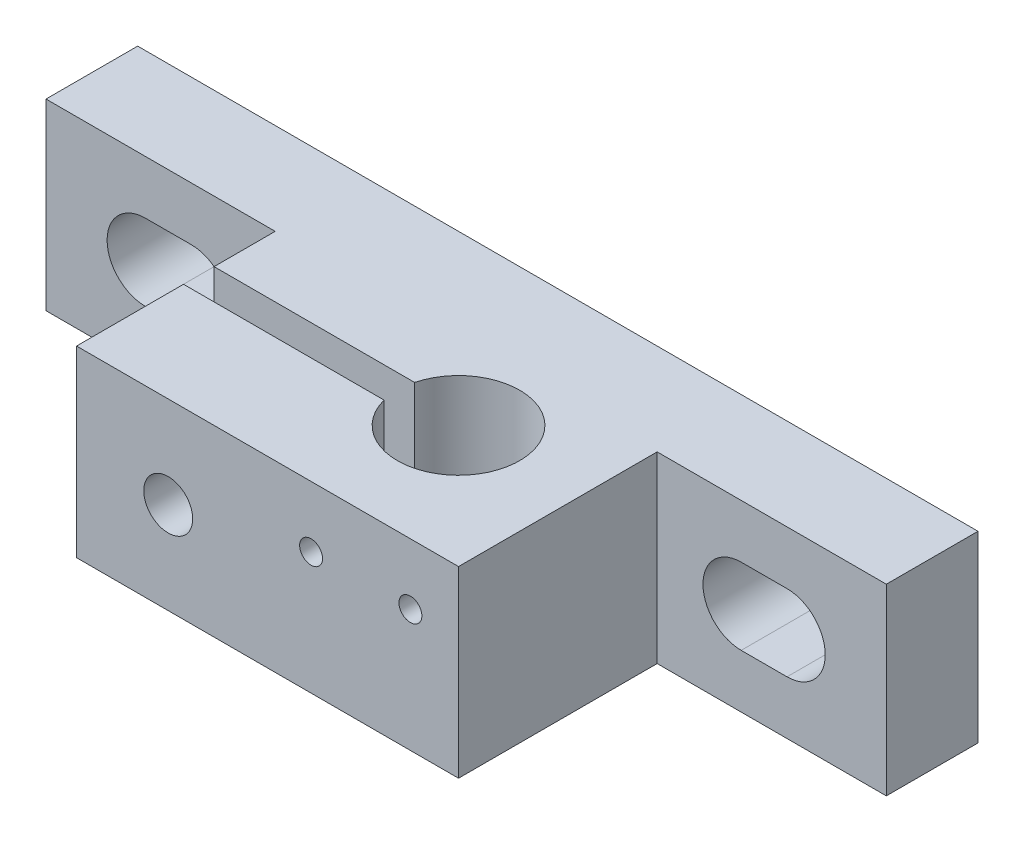
SolidWorks part; units mm, degrees
material "Copper"
ref_plane "Front Plane" through (0, 0, 0) normal (0, 0, 1) x (1, 0, 0)
ref_plane "Top Plane" through (0, 0, 0) normal (0, 1, 0) x (1, 0, 0)
ref_plane "Right Plane" through (0, 0, 0) normal (1, 0, 0) x (0, 0, -1)
sketch "Sketch2" plane through (0, 0, 0) normal (0, 0, 1) x (1, 0, 0)
  line L0 (6.5, 6) -> (9.5, 6) construction
  line L1 (0, 0) -> (55, 0)
  line L2 (0, 0) -> (0, 12)
  line L3 (0, 12) -> (55, 12)
  line L4 (55, 0) -> (55, 12)
  line L5 (27.5, 12) -> (27.5, -3.75) construction
  line L6 (6.5, 8.5) -> (9.5, 8.5)
  line L7 (6.5, 3.5) -> (9.5, 3.5)
  line L8 (48.5, 6) -> (45.5, 6) construction
  line L9 (48.5, 8.5) -> (45.5, 8.5)
  line L10 (48.5, 3.5) -> (45.5, 3.5)
  arc A0 (6.5, 8.5) -> (6.5, 3.5) centre (6.5, 6) ccw
  arc A1 (48.5, 8.5) -> (48.5, 3.5) centre (48.5, 6) cw
  arc A2 (9.5, 3.5) -> (9.5, 8.5) centre (9.5, 6) ccw
  arc A3 (45.5, 3.5) -> (45.5, 8.5) centre (45.5, 6) cw
  point P11 (8, 6)
  point P16 (47, 6)
  dimension "D1" = 6.5
  dimension "D2" = 3
  dimension "D5" = 55
extrude "Boss-Extrude1" add sketch "Sketch2" along normal blind 6
sketch "Sketch3" plane through (0, 0, 6) normal (0, 0, 1) x (1, 0, 0)
  line L0 (0, 0) -> (55, 0) construction
  line L1 (15, 0) -> (40, 0)
  line L2 (15, 0) -> (15, 12)
  line L3 (15, 12) -> (40, 12)
  line L4 (40, 0) -> (40, 12)
  line L5 (55, 12) -> (0, 12) construction
  line L6 (0, 12) -> (0, 0) construction
  line L7 (55, 0) -> (55, 12) construction
  dimension "D1" = 25
  dimension "D2" = 15
  dimension "D3" = 15
extrude "Boss-Extrude2" add sketch "Sketch3" along normal blind 13
sketch "Sketch4" plane through (0, 0, 0) normal (0, -1, 0) x (1, 0, 0)
  line L0 (15, 19) -> (40, 19) construction
  line L1 (40, 19) -> (40, 6) construction
  line L2 (0, 0) -> (55, 0) construction
  line L3 (28.127, 12) -> (15, 12)
  line L4 (15, 19) -> (15, 6) construction
  line L5 (15, 12) -> (15, 10)
  line L6 (15, 10) -> (28.127, 10)
  circle A0 centre (32, 11) radius 4
  line M4 (15, 19) -> (15, 6)
  dimension "D1" = 8
  dimension "D5" = 8
  dimension "D7" = 11
  dimension "D2" = 8
  dimension "D3" = 11
  dimension "D4" = 1
  dimension "D6" = 1
extrude "Cut-Extrude2" cut sketch "Sketch4" against normal blind 30 contours A0 L3 L6 M4 | A0
sketch "Sketch5" plane through (0, 0, 0) normal (0, 0, -1) x (-1, 0, 0)
  line L0 (-55, 12) -> (0, 12) construction
  line L1 (-37.6724, 9.5) -> (-17.1585, 9.5)
  line L2 (-37.6724, 9.5) -> (-37.6724, 2.5)
  line L3 (-37.6724, 2.5) -> (-17.1585, 2.5)
  line L4 (-17.1585, 9.5) -> (-17.1585, 2.5)
  line L5 (0, 0) -> (-55, 0) construction
  line L6 (0, 12) -> (0, 0) construction
  dimension "D1" = 20.5139
  dimension "D2" = 2.5
  dimension "D3" = 2.5
  dimension "D4" = 17.1585
extrude "Cut-Extrude3" cut sketch "Sketch5" against normal blind 5
sketch "Sketch6" plane through (0, 0, 19) normal (0, 0, 1) x (1, 0, 0)
  line L0 (15, 12) -> (15, 0) construction
  line L1 (40, 12) -> (15, 12) construction
  line L2 (15, 0) -> (40, 0) construction
  circle A0 centre (21, 6) radius 1.6
  dimension "D1" = 6
  dimension "D2" = 6
  dimension "D3" = 6
extrude "Cut-Extrude4" cut sketch "Sketch6" against normal blind 11
sketch "Sketch7" plane through (0, 0, 5) normal (0, 0, -1) x (-1, 0, 0)
  line L1 (-17.5359, 6) -> (-19.2679, 9)
  line L2 (-19.2679, 9) -> (-22.7321, 9)
  line L3 (-22.7321, 9) -> (-24.4641, 6)
  line L4 (-24.4641, 6) -> (-22.7321, 3)
  line L5 (-22.7321, 3) -> (-19.2679, 3)
  line L6 (-19.2679, 3) -> (-17.5359, 6)
  circle A0 centre (-21, 6) radius 3 construction
extrude "Cut-Extrude5" cut sketch "Sketch7" against normal blind 3
sketch "Sketch8" plane through (0, 0, 19) normal (0, 0, 1) x (1, 0, 0)
  line L0 (40, 0) -> (40, 12) construction
  line L1 (40, 12) -> (15, 12) construction
  circle A0 centre (36.85, 8) radius 0.75
  circle A1 centre (30.35, 8) radius 0.75
  dimension "D1" = 1.5
  dimension "D2" = 3.15
  dimension "D3" = 4
  dimension "D4" = 2
extrude "Cut-Extrude6" cut sketch "Sketch8" against normal blind 3
